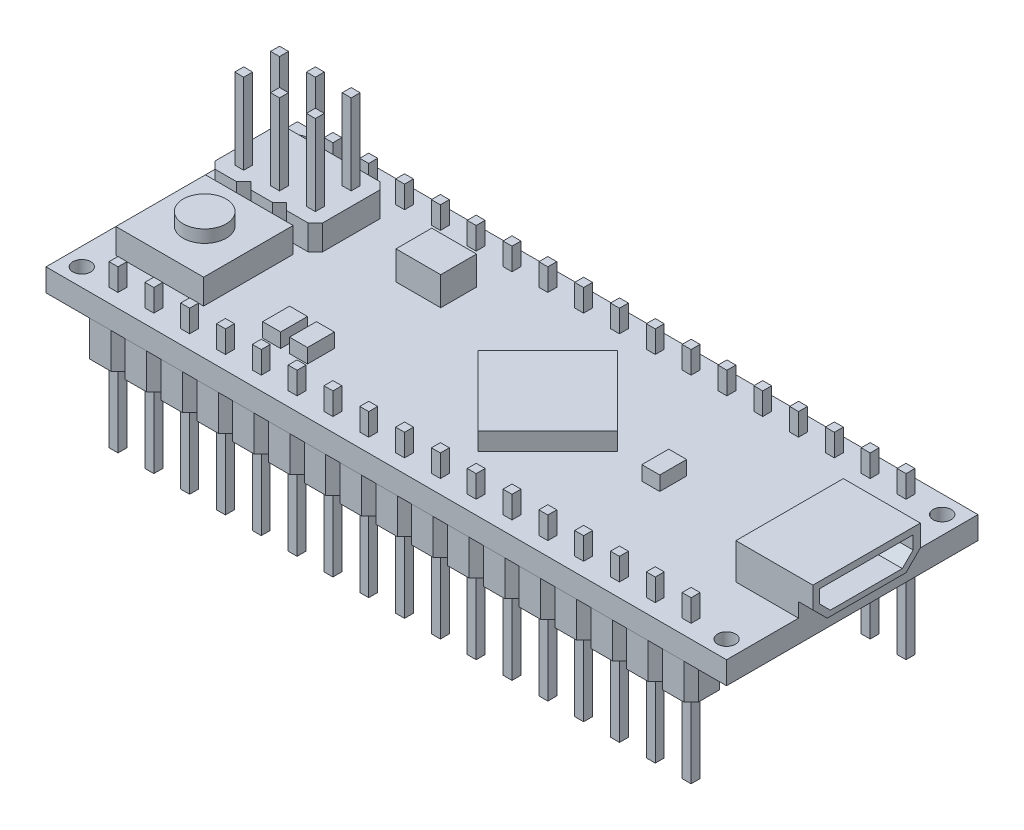
SolidWorks part; units mm, degrees
ref_plane "Front Plane" through (0, 0, 0) normal (0, 0, 1) x (1, 0, 0)
ref_plane "Top Plane" through (0, 0, 0) normal (0, 1, 0) x (1, 0, 0)
ref_plane "Right Plane" through (0, 0, 0) normal (1, 0, 0) x (0, 0, -1)
sketch "Sketch1" plane through (0, 0, 0) normal (0, 1, 0) x (1, 0, 0)
  line L1 (-24.13, -8.9154) -> (24.13, -8.9154)
  line L2 (-24.13, -8.9154) -> (-24.13, 8.9154)
  line L3 (-24.13, 8.9154) -> (24.13, 8.9154)
  line L4 (24.13, -8.9154) -> (24.13, 8.9154)
  line L5 (-24.13, -8.9154) -> (24.13, 8.9154) construction
  line L6 (-24.13, 8.9154) -> (24.13, -8.9154) construction
  point P0 (0, 0)
  dimension "D1" = 48.26
  dimension "D2" = 17.8308
extrude "Boss-Extrude1" add sketch "Sketch1" along normal blind 1.6002
sketch "Sketch2" plane through (0, 1.6002, 0) normal (0, 1, 0) x (1, 0, 0)
  line L0 (-2.3991, 0) -> (2.54, -4.9391)
  line L1 (-2.3991, 0) -> (2.54, 4.9391)
  line L2 (2.54, -4.9391) -> (7.4791, 0)
  line L3 (2.54, 4.9391) -> (7.4791, 0)
  line L4 (-2.3991, 0) -> (7.4791, 0) construction
  line L5 (2.54, -4.9391) -> (2.54, 4.9391) construction
  line L6 (24.13, -8.9154) -> (24.13, 8.9154) construction
  point P1 (2.54, 0)
  dimension "D1" = 6.985
  dimension "D2" = 21.59
extrude "Boss-Extrude2" add sketch "Sketch2" along normal blind 1.27
sketch "Sketch3" plane through (0, 1.6002, 0) normal (0, 1, 0) x (1, 0, 0)
  line L0 (-24.13, -8.9154) -> (24.13, -8.9154) construction
  line L1 (-22.352, 0.6096) -> (-16.129, 0.6096)
  line L2 (-22.352, 0.6096) -> (-22.352, -5.7404)
  line L3 (-22.352, -5.7404) -> (-16.129, -5.7404)
  line L4 (-16.129, 0.6096) -> (-16.129, -5.7404)
  line L5 (-24.13, 8.9154) -> (-24.13, -8.9154) construction
  dimension "D1" = 3.175
  dimension "D2" = 6.35
  dimension "D3" = 1.778
  dimension "D4" = 6.223
extrude "Boss-Extrude3" add sketch "Sketch3" along normal blind 1.778
sketch "Sketch4" plane through (0, 3.3782, 0) normal (0, 1, 0) x (1, 0, 0)
  line L0 (-16.129, 0.6096) -> (-22.352, -5.715) construction
  line L1 (-22.352, 0.6096) -> (-22.352, -5.7404) construction
  line L2 (-22.352, 0.6096) -> (-22.352, -5.7404) construction
  circle A0 centre (-19.2405, -2.5527) radius 1.524
  dimension "D1" = 3.048
extrude "Boss-Extrude4" add sketch "Sketch4" along normal blind 0.889
sketch "Sketch5" plane through (0, 1.6002, 0) normal (0, 1, 0) x (1, 0, 0)
  line L0 (0, 0) -> (19.685, 0) construction
  line L1 (19.685, 3.81) -> (25.146, 3.81)
  line L2 (19.685, 3.81) -> (19.685, -3.81)
  line L3 (19.685, -3.81) -> (25.146, -3.81)
  line L4 (25.146, 3.81) -> (25.146, -3.81)
  line L5 (24.13, -8.9154) -> (24.13, 8.9154) construction
  dimension "D1" = 4.445
  dimension "D2" = 7.62
  dimension "D3" = 5.461
extrude "Boss-Extrude5" add sketch "Sketch5" along normal blind 2.54
sketch "Sketch6" plane through (25.146, 0, 0) normal (1, 0, 0) x (0, 0, -1)
  line L0 (-3.3328, 2.745) -> (-2.5708, 1.983)
  line L1 (-3.3328, 3.6776) -> (3.2952, 3.6776)
  line L2 (-3.3328, 3.6776) -> (-3.3328, 2.745)
  line L3 (-2.5708, 1.983) -> (2.5332, 1.983)
  line L4 (3.2952, 3.6776) -> (3.2952, 2.745)
  line L5 (2.5332, 1.983) -> (3.2952, 2.745)
  point P1 (3.2952, 1.983)
  point P2 (-3.3328, 1.983)
extrude "Cut-Extrude1" cut sketch "Sketch6" against normal blind 4.318
sketch "Sketch7" plane through (0, 1.6002, 0) normal (0, 1, 0) x (1, 0, 0)
  line L0 (-24.13, 8.9154) -> (-24.13, -8.9154) construction
  line L1 (-22.352, 6.3754) -> (-20.828, 6.3754)
  line L2 (-22.86, 5.8674) -> (-22.86, 1.8034)
  line L3 (-22.352, 1.2954) -> (-20.828, 1.2954)
  line L4 (-20.32, 5.8674) -> (-20.32, 1.8034)
  line L5 (24.13, 8.9154) -> (-24.13, 8.9154) construction
  line L6 (-22.86, 1.8034) -> (-22.352, 1.2954)
  line L7 (-20.828, 1.2954) -> (-20.32, 1.8034)
  line L8 (-20.828, 6.3754) -> (-20.32, 5.8674)
  line L9 (-22.86, 5.8674) -> (-22.352, 6.3754)
  point P0 (-22.86, 6.3754)
  point P1 (-20.32, 1.2954)
  point P2 (-22.86, 1.2954)
  point P3 (-20.32, 6.3754)
  dimension "D1" = 5.08
  dimension "D2" = 2.54
  dimension "D3" = 1.27
  dimension "D4" = 2.54
extrude "Boss-Extrude6" add sketch "Sketch7" along normal blind 1.778
sketch "Sketch8" plane through (0, 3.3782, 0) normal (0, 1, 0) x (1, 0, 0)
  line L0 (-20.32, 1.8034) -> (-20.32, 5.8674) construction
  line L1 (-21.9075, 4.7879) -> (-21.2725, 4.7879)
  line L2 (-21.9075, 4.7879) -> (-21.9075, 5.4229)
  line L3 (-21.9075, 5.4229) -> (-21.2725, 5.4229)
  line L4 (-21.2725, 4.7879) -> (-21.2725, 5.4229)
  line L5 (-21.9075, 4.7879) -> (-21.2725, 5.4229) construction
  line L6 (-21.9075, 5.4229) -> (-21.2725, 4.7879) construction
  line L7 (-21.9075, 2.2479) -> (-21.2725, 2.2479)
  line L8 (-21.9075, 2.2479) -> (-21.9075, 2.8829)
  line L9 (-21.9075, 2.8829) -> (-21.2725, 2.8829)
  line L10 (-21.2725, 2.2479) -> (-21.2725, 2.8829)
  line L11 (-21.9075, 2.2479) -> (-21.2725, 2.8829) construction
  line L12 (-21.9075, 2.8829) -> (-21.2725, 2.2479) construction
  line L13 (-22.352, 1.2954) -> (-20.828, 1.2954) construction
  point P0 (-21.59, 5.1054)
  point P5 (-21.59, 2.5654)
  dimension "D1" = 0.635
  dimension "D2" = 2.54
  dimension "D3" = 1.27
  dimension "D4" = 1.27
extrude "Boss-Extrude7" add sketch "Sketch8" along normal blind 5.715
pattern_linear "LPattern1" count 3 spacing 2.54 along (1, 0, 0) of "Boss-Extrude6", "Boss-Extrude7"
sketch "Sketch9" plane through (0, 1.6002, 0) normal (0, 1, 0) x (1, 0, 0)
  line L0 (24.13, 8.9154) -> (-24.13, 8.9154) construction
  line L1 (-22.86, 7.6454) -> (22.86, 7.6454) construction
  line L2 (-22.86, 7.6454) -> (-22.86, -7.6454) construction
  line L3 (-22.86, -7.6454) -> (22.86, -7.6454) construction
  line L4 (22.86, 7.6454) -> (22.86, -7.6454) construction
  line L5 (-24.13, -8.9154) -> (24.13, -8.9154) construction
  line L6 (24.13, -8.9154) -> (24.13, -3.81) construction
  line L7 (-24.13, 8.9154) -> (-24.13, -8.9154) construction
  circle A0 centre (-22.86, 7.6454) radius 0.635
  circle A1 centre (-22.86, -7.6454) radius 0.635
  circle A2 centre (22.86, -7.6454) radius 0.635
  circle A3 centre (22.86, 7.6454) radius 0.635
  dimension "D5" = 1.27
  dimension "D1" = 1.27
  dimension "D2" = 1.27
  dimension "D3" = 1.27
  dimension "D4" = 1.27
extrude "Cut-Extrude2" cut sketch "Sketch9" against normal through all
sketch "Sketch10" plane through (0, 0, 0) normal (0, -1, 0) x (1, 0, 0)
  line L0 (-21.59, 6.858) -> (-21.082, 6.35)
  line L1 (-21.082, 6.35) -> (-19.558, 6.35)
  line L2 (-21.59, 6.858) -> (-21.59, 8.382)
  line L3 (-21.082, 8.89) -> (-19.558, 8.89)
  line L4 (-19.05, 6.858) -> (-19.05, 8.382)
  line L5 (-19.558, 6.35) -> (-19.05, 6.858)
  line L6 (-19.558, 8.89) -> (-19.05, 8.382)
  line L7 (-21.59, 8.382) -> (-21.082, 8.89)
  line L10 (-24.13, -8.9154) -> (-24.13, 8.9154) construction
  line L12 (-24.13, 8.9154) -> (24.13, 8.9154) construction
  point P0 (-21.59, 6.35)
  point P1 (-19.05, 8.89)
  point P2 (-21.59, 8.89)
  point P3 (-19.05, 6.35)
  dimension "D1" = 2.54
  dimension "D2" = 2.54
  dimension "D3" = 2.54
  dimension "D4" = 0.0254
extrude "Boss-Extrude8" add sketch "Sketch10" along normal blind 2.54
sketch "Sketch11" plane through (0, -2.54, 0) normal (0, -1, 0) x (1, 0, 0)
  line L0 (-19.05, 6.858) -> (-19.05, 8.382) construction
  line L1 (-20.6375, 7.9375) -> (-20.0025, 7.9375)
  line L2 (-20.6375, 7.9375) -> (-20.6375, 7.3025)
  line L3 (-20.6375, 7.3025) -> (-20.0025, 7.3025)
  line L4 (-20.0025, 7.9375) -> (-20.0025, 7.3025)
  line L5 (-20.6375, 7.9375) -> (-20.0025, 7.3025) construction
  line L6 (-20.6375, 7.3025) -> (-20.0025, 7.9375) construction
  line L7 (-21.082, 6.35) -> (-19.558, 6.35) construction
  point P0 (-20.32, 7.62)
  dimension "D1" = 0.635
  dimension "D2" = 1.27
  dimension "D3" = 1.27
extrude "Boss-Extrude9" add sketch "Sketch11" along normal blind 5.715 and the other way blind 5.715
pattern_linear "LPattern2" count 17 spacing 2.54 along (1, 0, 0) count 2 spacing 15.24 along (0, 0, -1) of "Boss-Extrude9", "Boss-Extrude8"
sketch "Sketch12" plane through (0, 1.6002, 0) normal (0, 1, 0) x (1, 0, 0)
  line L0 (-24.13, 8.9154) -> (-24.13, -8.9154) construction
  line L1 (-12.065, -5.6134) -> (-10.795, -5.6134)
  line L2 (-12.065, -5.6134) -> (-12.065, -3.7084)
  line L3 (-12.065, -3.7084) -> (-10.795, -3.7084)
  line L4 (-10.795, -5.6134) -> (-10.795, -3.7084)
  line L5 (-12.065, -5.6134) -> (-10.795, -3.7084) construction
  line L6 (-12.065, -3.7084) -> (-10.795, -5.6134) construction
  line L7 (-10.16, -5.6134) -> (-8.89, -5.6134)
  line L8 (-10.16, -5.6134) -> (-10.16, -3.7084)
  line L9 (-10.16, -3.7084) -> (-8.89, -3.7084)
  line L10 (-8.89, -5.6134) -> (-8.89, -3.7084)
  line L11 (-10.16, -5.6134) -> (-8.89, -3.7084) construction
  line L12 (-10.16, -3.7084) -> (-8.89, -5.6134) construction
  line L13 (-24.13, -8.9154) -> (24.13, -8.9154) construction
  point P0 (-11.43, -4.6609)
  point P5 (-9.525, -4.6609)
  dimension "D1" = 12.7
  dimension "D2" = 1.27
  dimension "D3" = 0.635
  dimension "D4" = 1.905
  dimension "D5" = 3.302
extrude "Boss-Extrude10" add sketch "Sketch12" along normal blind 1.016
sketch "Sketch13" plane through (0, 1.6002, 0) normal (0, 1, 0) x (1, 0, 0)
  line L0 (19.685, 3.81) -> (19.685, -3.81) construction
  line L1 (10.16, 0.9525) -> (11.43, 0.9525)
  line L2 (10.16, 0.9525) -> (10.16, -0.9525)
  line L3 (10.16, -0.9525) -> (11.43, -0.9525)
  line L4 (11.43, 0.9525) -> (11.43, -0.9525)
  line L5 (10.16, 0.9525) -> (11.43, -0.9525) construction
  line L6 (10.16, -0.9525) -> (11.43, 0.9525) construction
  point P0 (10.795, 0)
  dimension "D1" = 1.27
  dimension "D2" = 1.905
  dimension "D3" = 8.89
extrude "Boss-Extrude11" add sketch "Sketch13" along normal blind 1.016
sketch "Sketch14" plane through (0, 1.6002, 0) normal (0, 1, 0) x (1, 0, 0)
  line L1 (-7.62, 2.5654) -> (-10.795, 2.5654)
  line L2 (-7.62, 2.5654) -> (-7.62, 5.1054)
  line L3 (-7.62, 5.1054) -> (-10.795, 5.1054)
  line L4 (-10.795, 2.5654) -> (-10.795, 5.1054)
  line L5 (-7.62, 2.5654) -> (-10.795, 5.1054) construction
  line L6 (-7.62, 5.1054) -> (-10.795, 2.5654) construction
  line L7 (-15.24, 1.8034) -> (-15.24, 5.8674) construction
  line L8 (24.13, 8.9154) -> (-24.13, 8.9154) construction
  point P0 (-9.2075, 3.8354)
  dimension "D1" = 3.175
  dimension "D2" = 2.54
  dimension "D3" = 4.445
  dimension "D4" = 3.81
extrude "Boss-Extrude12" add sketch "Sketch14" along normal blind 2.032
chamfer "Chamfer1" distance 1.016 angle 45 2 edges at (24.638, 1.6002, -3.81) (24.638, 1.6002, 3.81)
